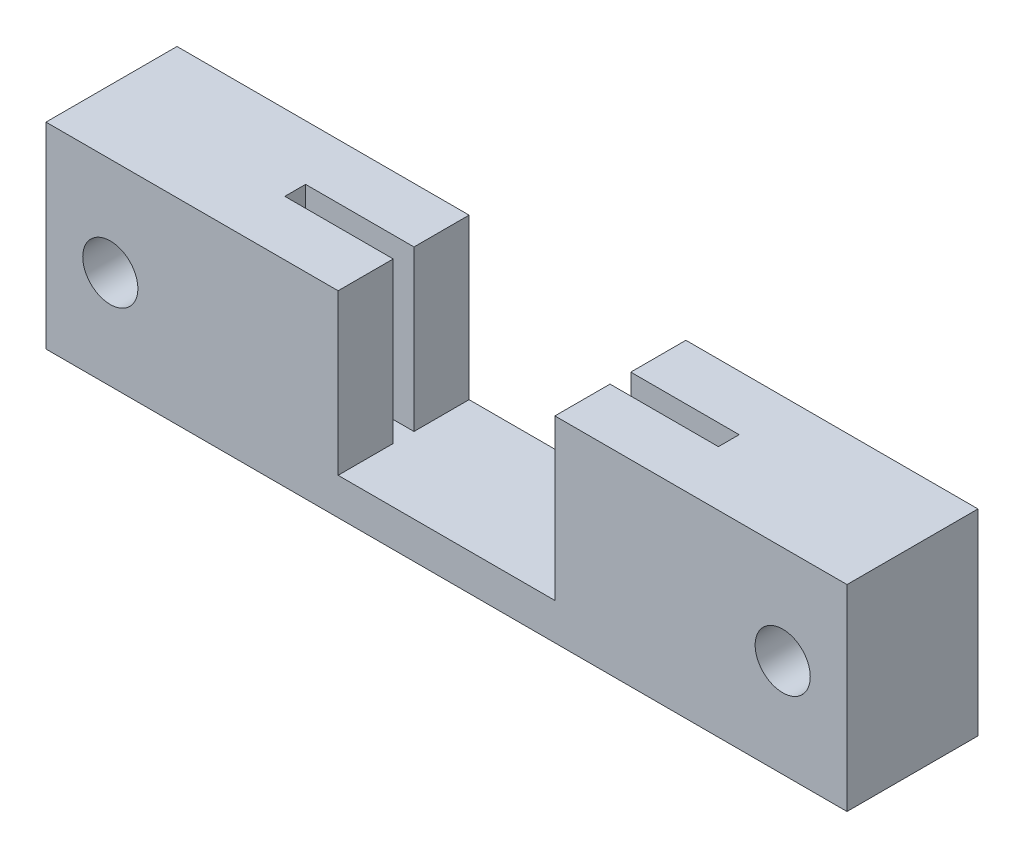
SolidWorks part; units mm, degrees
ref_plane "Front Plane" through (0, 0, 0) normal (0, 0, 1) x (1, 0, 0)
ref_plane "Top Plane" through (0, 0, 0) normal (0, 1, 0) x (1, 0, 0)
ref_plane "Right Plane" through (0, 0, 0) normal (1, 0, 0) x (0, 0, -1)
sketch "Sketch2" plane through (0, 0, 0) normal (0, 1, 0) x (1, 0, 0)
  line L0 (5.9, 3.565) -> (14.8, 3.565)
  line L1 (5.9, 0.565) -> (11.8, 0.565)
  line L3 (5.9, -0.565) -> (11.8, -0.565)
  line L4 (11.8, 0.565) -> (11.8, -0.565)
  line L5 (14.8, 3.565) -> (14.8, -3.565)
  line L6 (5.9, -3.565) -> (14.8, -3.565)
  line L8 (5.9, 0.565) -> (5.9, 3.565)
  line L9 (5.9, -0.565) -> (5.9, -3.565)
  line L10 (2.9, -3.565) -> (14.8, -3.565) construction
  line L11 (2.9, 3.565) -> (2.9, -3.565) construction
  line L12 (2.9, 3.565) -> (14.8, 3.565) construction
  line L13 (5.9, 3.565) -> (5.9, 0.565)
  line L14 (5.9, -0.565) -> (5.9, -3.565)
  line L15 (0, 0) -> (0, 6.6462) construction
  line L16 (5.9, 0.565) -> (5.9, -0.565) construction
  line L17 (-5.9, -0.565) -> (-5.9, -3.565)
  line L18 (-5.9, 3.565) -> (-5.9, 0.565)
  line L19 (-5.9, -0.565) -> (-5.9, -3.565)
  line L20 (-5.9, 0.565) -> (-5.9, 3.565)
  line L21 (-5.9, -3.565) -> (-14.8, -3.565)
  line L22 (-14.8, 3.565) -> (-14.8, -3.565)
  line L23 (-11.8, 0.565) -> (-11.8, -0.565)
  line L24 (-5.9, -0.565) -> (-11.8, -0.565)
  line L25 (-5.9, 0.565) -> (-11.8, 0.565)
  line L26 (-5.9, 3.565) -> (-14.8, 3.565)
  point P4 (11.8, 0)
  point P18 (-11.8, 0)
  dimension "D1" = 5.9
  dimension "D2" = 1.13
  dimension "D4" = 11.8
  dimension "D3" = 3
extrude "Boss-Extrude1" add sketch "Sketch2" along normal blind 8.7 contours L18 L26 L22 L21 L17 L24 L23 L25 | L3 L9 L6 L5 L0 L8 L1 L4
sketch "Sketch3" plane through (0, 0, 0) normal (0, -1, 0) x (1, 0, 0)
  line L0 (14.8, -3.565) -> (14.8, 3.565) construction
  line L1 (-14.8, 3.565) -> (14.8, 3.565)
  line L2 (-14.8, 3.565) -> (-14.8, -3.565)
  line L3 (-14.8, -3.565) -> (14.8, -3.565)
  line L4 (14.8, 3.565) -> (14.8, -3.565)
  line L5 (5.9, -3.565) -> (14.8, -3.565) construction
extrude "Boss-Extrude2" add sketch "Sketch3" along normal blind 2
sketch "Sketch4" plane through (0, 0, 3.565) normal (0, 0, 1) x (1, 0, 0)
  line L0 (14.8, -2) -> (-14.8, -2) construction
  line L1 (14.8, 8.7) -> (21.8, 8.7)
  line L2 (14.8, 8.7) -> (14.8, -2)
  line L3 (14.8, -2) -> (21.8, -2)
  line L4 (21.8, 8.7) -> (21.8, -2)
  line L5 (0, 0) -> (0, 8.9854) construction
  line L6 (21.8, 8.7) -> (14.8, -2) construction
  line L7 (-21.8, 8.7) -> (-14.8, -2) construction
  line L8 (-21.8, 8.7) -> (-21.8, -2)
  line L9 (-14.8, -2) -> (-21.8, -2)
  line L10 (-14.8, 8.7) -> (-14.8, -2)
  line L11 (-14.8, 8.7) -> (-21.8, 8.7)
  circle A0 centre (18.3, 3.35) radius 1.5
  circle A1 centre (-18.3, 3.35) radius 1.5
  dimension "D2" = 3
  dimension "D1" = 7
extrude "Boss-Extrude3" add sketch "Sketch4" against normal blind 7.13
